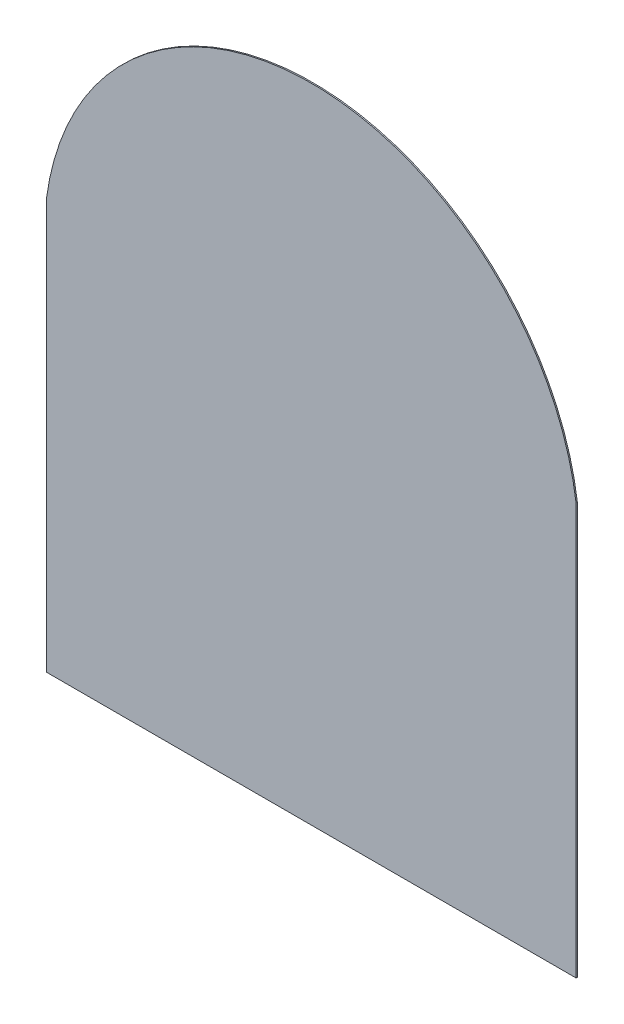
SolidWorks part; units mm, degrees
ref_plane "Front Plane" through (0, 0, 0) normal (0, 0, 1) x (1, 0, 0)
ref_plane "Top Plane" through (0, 0, 0) normal (0, 1, 0) x (1, 0, 0)
ref_plane "Right Plane" through (0, 0, 0) normal (1, 0, 0) x (0, 0, -1)
sketch "Sketch1" plane through (0, 0, 0) normal (0, 0, 1) x (1, 0, 0)
  line L2 (1030, 800) -> (1030, -800)
  line L3 (1030, -800) -> (-1030, -800)
  line L4 (-1030, 800) -> (-1030, -800)
  line L5 (1030, 800) -> (-1030, -800) construction
  line L6 (1030, -800) -> (-1030, 800) construction
  arc A1 (-1030, 800) -> (1030, 800) centre (0, 660.6111) cw
  point P0 (0, 0)
  point P1 (0, 0)
  point P8 (0, 0)
  point P9 (0, 0)
  point P10 (0, 1700)
  dimension "D1" = 2060
  dimension "D2" = 900
  dimension "D3" = 1600
extrude "Boss-Extrude1" add sketch "Sketch1" along normal mid plane 5
